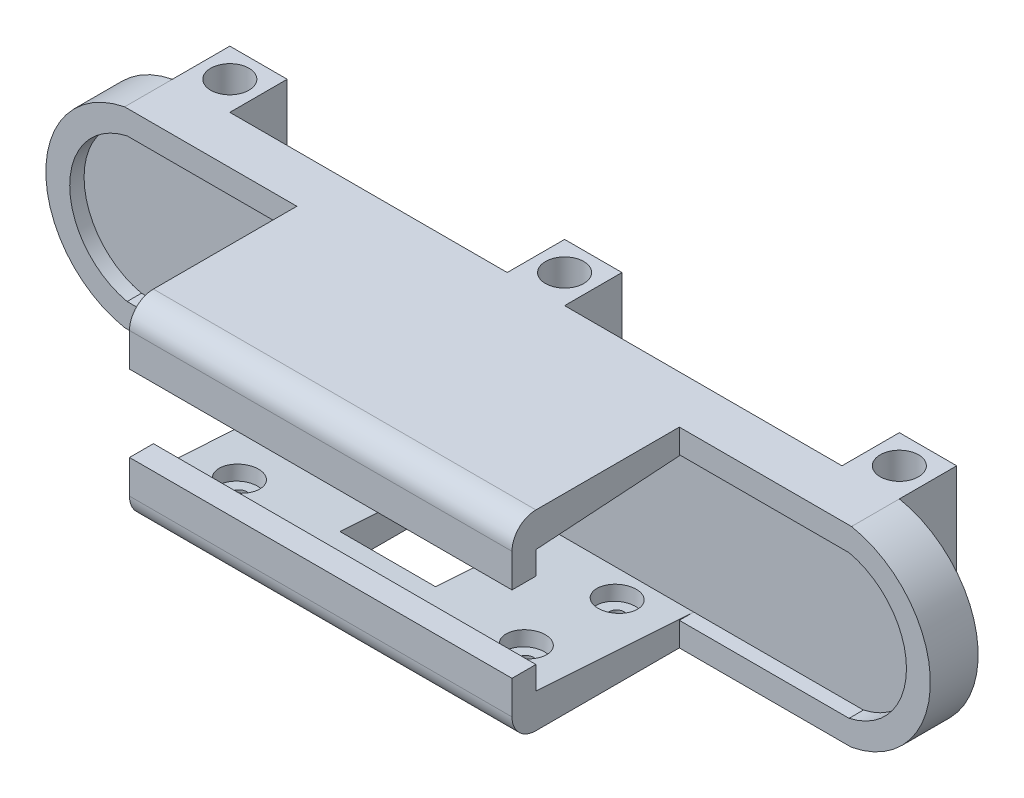
SolidWorks part; units mm, degrees
material "PMMA"
ref_plane "Front Plane" through (0, 0, 0) normal (0, 0, 1) x (1, 0, 0)
ref_plane "Top Plane" through (0, 0, 0) normal (0, 1, 0) x (1, 0, 0)
ref_plane "Right Plane" through (0, 0, 0) normal (1, 0, 0) x (0, 0, -1)
sketch "Schizzo1" plane through (0, 0, 0) normal (0, 0, 1) x (1, 0, 0)
  line L0 (-75.5, -15) -> (75.5, -15) construction
  line L1 (-75.5, 15) -> (75.5, 15) construction
  line L2 (-87.5, 15) -> (-87.5, -15) construction
  line L5 (87.5, 15) -> (87.5, -15) construction
  line L6 (-87.5, -15) -> (87.5, -15) construction
  line L7 (-75.5, 15) -> (-75.5, -15) construction
  line L8 (-87.5, 15) -> (87.5, 15) construction
  line L9 (-75.5, 15) -> (75.5, -15) construction
  line L10 (-76.0161, 20) -> (76.0161, 20)
  line L11 (-76.0161, -20) -> (76.0161, -20)
  arc A0 (-75.5, 15) -> (-75.5, -15) centre (-72.125, 0) ccw construction
  arc A1 (75.5, 15) -> (75.5, -15) centre (72.125, 0) cw construction
  arc A2 (76.0161, 20) -> (76.0161, -20) centre (72.125, 0) cw
  arc A3 (-76.0161, 20) -> (-76.0161, -20) centre (-72.125, 0) ccw
  point P12 (0, -15)
  point P13 (0, -15)
  point P14 (0, 0)
  dimension "D2" = 175
  dimension "D3" = 30
  dimension "D1" = 151
  dimension "D4" = 5
extrude "Estrusione-Estrusione1" add sketch "Schizzo1" along normal blind 10
sketch "Schizzo3" plane through (0, 0, 10) normal (0, 0, 1) x (1, 0, 0)
  line L0 (-75.5, -15) -> (75.5, -15)
  line L1 (-75.5, 15) -> (75.5, 15)
  line L2 (-87.5, 15) -> (-87.5, -15) construction
  line L3 (87.5, 15) -> (87.5, -15) construction
  line L4 (-87.5, -15) -> (87.5, -15) construction
  line L5 (-75.5, 15) -> (-75.5, -15) construction
  line L6 (-87.5, 15) -> (87.5, 15) construction
  line L7 (-75.5, 15) -> (75.5, -15) construction
  line L8 (-75.5, 15) -> (-75.5, -15) construction
  line L9 (-75.5, 15) -> (75.5, 15) construction
  arc A0 (-75.5, 15) -> (-75.5, -15) centre (-72.125, 0) ccw
  arc A1 (75.5, 15) -> (75.5, -15) centre (72.125, 0) cw
  point P12 (0, -15)
  point P13 (0, -15)
  dimension "D3" = 30
  dimension "D1" = 151
  dimension "D2" = 175
extrude "Taglio-Estrusione1" cut sketch "Schizzo3" against normal blind 3
sketch "Schizzo4" plane through (0, 0, 10) normal (0, 0, 1) x (1, 0, 0)
  line L1 (-40, -15) -> (40, -15)
  line L2 (-40, -15) -> (-40, -20)
  line L3 (-40, -20) -> (40, -20)
  line L4 (40, -15) -> (40, -20)
  line L7 (-75.5, -15) -> (75.5, -15) construction
  line L8 (-76.0161, -20) -> (76.0161, -20) construction
  point P8 (0, -20)
  dimension "D1" = 80
extrude "Estrusione-Estrusione2" add sketch "Schizzo4" along normal blind 35
sketch "Schizzo6" plane through (40, 0, 0) normal (1, 0, 0) x (0, 0, -1)
  line L0 (-40, -15) -> (-40, -12.81)
  line L1 (-45, -15) -> (-10, -15) construction
  line L2 (-40, -12.81) -> (-7, -15)
  line L3 (-7, -15) -> (-40, -15)
  line L4 (-45, -20) -> (-45, -15) construction
  dimension "D1" = 2.19
  dimension "D2" = 5
extrude "Estrusione-Estrusione4" add sketch "Schizzo6" against normal blind 80
sketch "Schizzo7" plane through (0, -15, 0) normal (0, 1, 0) x (1, 0, 0)
  line L1 (-40, -40) -> (40, -40)
  line L2 (-40, -40) -> (-40, -45)
  line L3 (-40, -45) -> (40, -45)
  line L4 (40, -40) -> (40, -45)
  dimension "D1" = 5
  dimension "D2" = 80
extrude "Estrusione-Estrusione5" add sketch "Schizzo7" along normal blind 7
sketch "Schizzo8" plane through (0, -20, 0) normal (0, -1, 0) x (1, 0, 0)
  line L0 (-40, 45) -> (-40, 10) construction
  line L2 (-76.0161, 0) -> (76.0161, 0) construction
  line L3 (-40, 45) -> (40, 45) construction
  line L4 (0, 45) -> (0, 0) construction
  circle A0 centre (-30, 13) radius 1.5
  circle A1 centre (-30, 32) radius 1.5
  circle A2 centre (30, 13) radius 1.5
  circle A3 centre (30, 32) radius 1.5
  dimension "D1" = 3
  dimension "D4" = 13
  dimension "D2" = 10
  dimension "D3" = 13
  dimension "D5" = 10
  dimension "D6" = 30
  dimension "D7" = 19
extrude "Taglio-Estrusione2" cut sketch "Schizzo8" against normal up to next
mirror "Specchia1" about plane through (0, 0, 0) normal (0, 1, 0) of "Estrusione-Estrusione2", "Estrusione-Estrusione4", "Estrusione-Estrusione5"
fillet "Raccordo1" radius 5 1 edges at (0, -20, 45)
fillet "Raccordo2" radius 5 1 edges at (0, 20, 45)
sketch "Schizzo9" plane through (0, -20, 0) normal (0, -1, 0) x (1, 0, 0)
  line L0 (-4, 11) -> (-4, 3)
  line L1 (-4, 3) -> (4, 3)
  line L2 (4, 3) -> (4, 11)
  line L3 (4, 11) -> (10, 11)
  line L4 (10, 11) -> (10, 31)
  line L5 (10, 31) -> (-10, 31)
  line L6 (-10, 31) -> (-10, 11)
  line L7 (-10, 11) -> (-4, 11)
  line L8 (0, 40) -> (0, 0) construction
  line L9 (40, 40) -> (-40, 40) construction
  line L10 (-76.0161, 0) -> (76.0161, 0) construction
  point P13 (0, 31)
  point P14 (0, 3)
  dimension "D1" = 8
  dimension "D2" = 3
  dimension "D3" = 20
  dimension "D4" = 20
  dimension "D5" = 8
extrude "Taglio-Estrusione3" cut sketch "Schizzo9" against normal blind 10 and the other way through all
sketch "Schizzo11" plane through (0, -15.3967, 1.0218) normal (0, 0.9978, -0.0662) x (1, 0, 0)
  circle A0 centre (-30, -12.0046) radius 4
  circle A1 centre (-30, -31.0464) radius 4
  circle A2 centre (30, -31.0464) radius 4
  circle A3 centre (30, -12.0046) radius 4
  ellipse E0 centre (-30, -12.0046) end of major axis (-30, -10.5013) minor radius 1.5 construction
  ellipse E1 centre (-30, -31.0464) end of major axis (-30, -32.5497) minor radius 1.5 construction
  ellipse E2 centre (30, -12.0046) end of major axis (30, -10.5013) minor radius 1.5 construction
  ellipse E3 centre (30, -31.0464) end of major axis (30, -29.5431) minor radius 1.5 construction
  dimension "D1" = 8
extrude "Taglio-Estrusione4" cut sketch "Schizzo11" against normal blind 3
sketch "Schizzo12" plane through (0, -20, 0) normal (0, -1, 0) x (1, 0, 0)
  line L0 (-76.0161, 10) -> (-76.0161, 0) construction
  line L1 (-76.0161, 0) -> (76.0161, 0) construction
  line L2 (76.0161, 0) -> (64.0161, 0)
  line L3 (76.0161, 0) -> (76.0161, -12)
  line L4 (76.0161, -12) -> (64.0161, -12)
  line L5 (64.0161, 0) -> (64.0161, -12)
  line L6 (76.0161, 10) -> (76.0161, 0) construction
  line L7 (-64.0161, 0) -> (-76.0161, 0)
  line L8 (-64.0161, 0) -> (-64.0161, -12)
  line L9 (-64.0161, -12) -> (-76.0161, -12)
  line L10 (-76.0161, 0) -> (-76.0161, -12)
  line L11 (6, 0) -> (-6, 0)
  line L12 (6, 0) -> (6, -12)
  line L13 (6, -12) -> (-6, -12)
  line L14 (-6, 0) -> (-6, -12)
  point P18 (0, 0)
  dimension "D1" = 12
  dimension "D2" = 12
  dimension "D3" = 12
  dimension "D4" = 12
  dimension "D5" = 12
  dimension "D6" = 12
extrude "Estrusione-Estrusione6" add sketch "Schizzo12" against normal up to surface (40 mm away) up to face at (0, 20, 15)
sketch "Schizzo13" plane through (0, -20, 0) normal (0, -1, 0) x (1, 0, 0)
  line L0 (-76.0161, -6) -> (76.0161, -6) construction
  line L1 (-76.0161, 0) -> (-76.0161, -12) construction
  line L2 (76.0161, -12) -> (76.0161, 0) construction
  line L3 (-70.0161, -12) -> (-70.0161, 10) construction
  line L4 (-76.0161, -12) -> (-64.0161, -12) construction
  line L5 (-76.0161, 10) -> (-40, 10) construction
  line L6 (0, -12) -> (0, 3) construction
  line L7 (-6, -12) -> (6, -12) construction
  line L8 (-4, 3) -> (4, 3) construction
  line L9 (70.0161, -12) -> (70.0161, 10) construction
  line L10 (64.0161, -12) -> (76.0161, -12) construction
  line L11 (40, 10) -> (76.0161, 10) construction
  circle A0 centre (-70.0161, -6) radius 1.5
  circle A1 centre (0, -6) radius 1.5
  circle A2 centre (70.0161, -6) radius 1.5
  dimension "D1" = 3
extrude "Taglio-Estrusione5" cut sketch "Schizzo13" against normal through all
sketch "Schizzo14" plane through (0, -20, 0) normal (0, -1, 0) x (1, 0, 0)
  circle A0 centre (-70.0161, -6) radius 4
  circle A1 centre (-70.0161, -6) radius 1.5 construction
  circle A2 centre (0, -6) radius 4
  circle A3 centre (70.0161, -6) radius 4
  circle A4 centre (70.0161, -6) radius 1.5 construction
  circle A5 centre (0, -6) radius 1.5 construction
  dimension "D1" = 8
extrude "Taglio-Estrusione6" cut sketch "Schizzo14" against normal blind 10
mirror "Specchia2" about plane through (0, 0, 0) normal (0, 1, 0) of "Taglio-Estrusione6"
